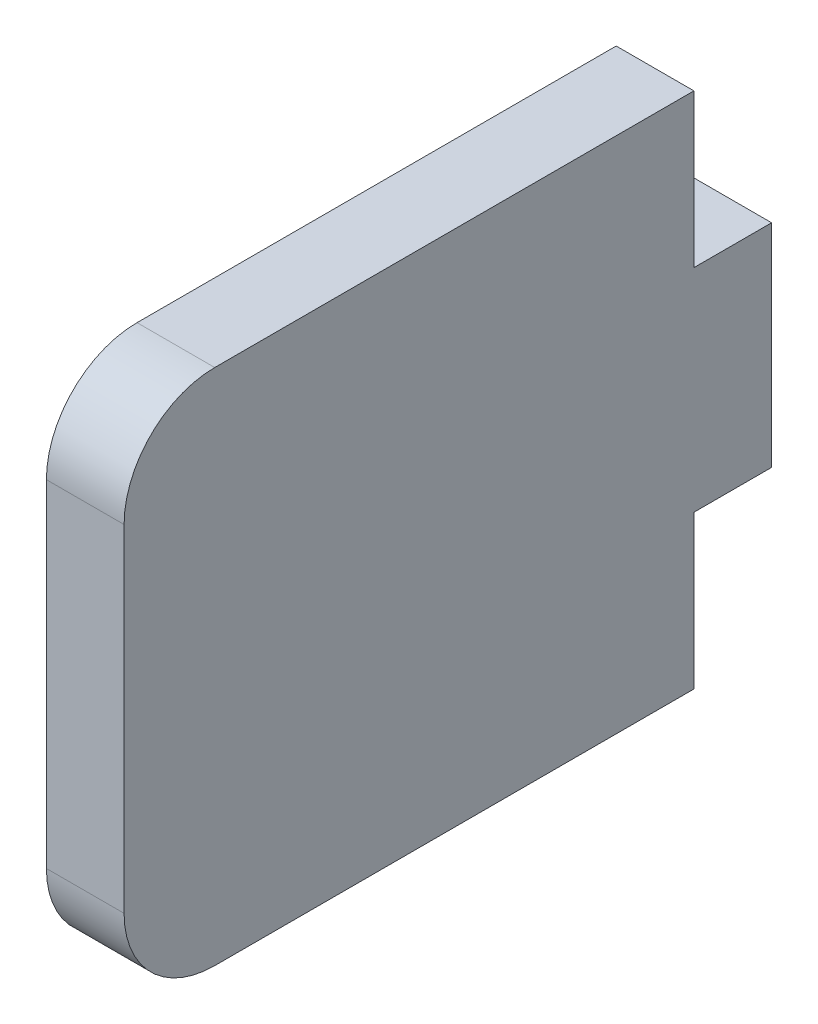
SolidWorks part; units mm, degrees
ref_plane "Front Plane" through (0, 0, 0) normal (0, 0, 1) x (1, 0, 0)
ref_plane "Top Plane" through (0, 0, 0) normal (0, 1, 0) x (1, 0, 0)
ref_plane "Right Plane" through (0, 0, 0) normal (1, 0, 0) x (0, 0, -1)
sketch "Sketch1" plane through (0, 0, 0) normal (1, 0, 0) x (0, 0, -1)
  line L0 (-11, 10) -> (11, 10)
  line L1 (11, 10) -> (11, 4.09)
  line L2 (11, 4.09) -> (14, 4.09)
  line L3 (14, 4.09) -> (14, -4.09)
  line L4 (14, -4.09) -> (11, -4.09)
  line L5 (11, -4.09) -> (11, -10)
  line L6 (11, -10) -> (-11, -10)
  line L7 (-11, -10) -> (-11, 10)
  point P4 (0, 10)
  point P9 (0, -10)
  point P11 (-11, 0)
  point P12 (14, 0)
  point P13 (15.1408, 4.09)
  dimension "D1" = 20
  dimension "D2" = 3
  dimension "D3" = 8.18
  dimension "D4" = 22
extrude "Boss-Extrude1" add sketch "Sketch1" along normal blind 3
fillet "Fillet1" radius 3.5 2 edges at (1.5, -10, 11) (1.5, 10, 11)
